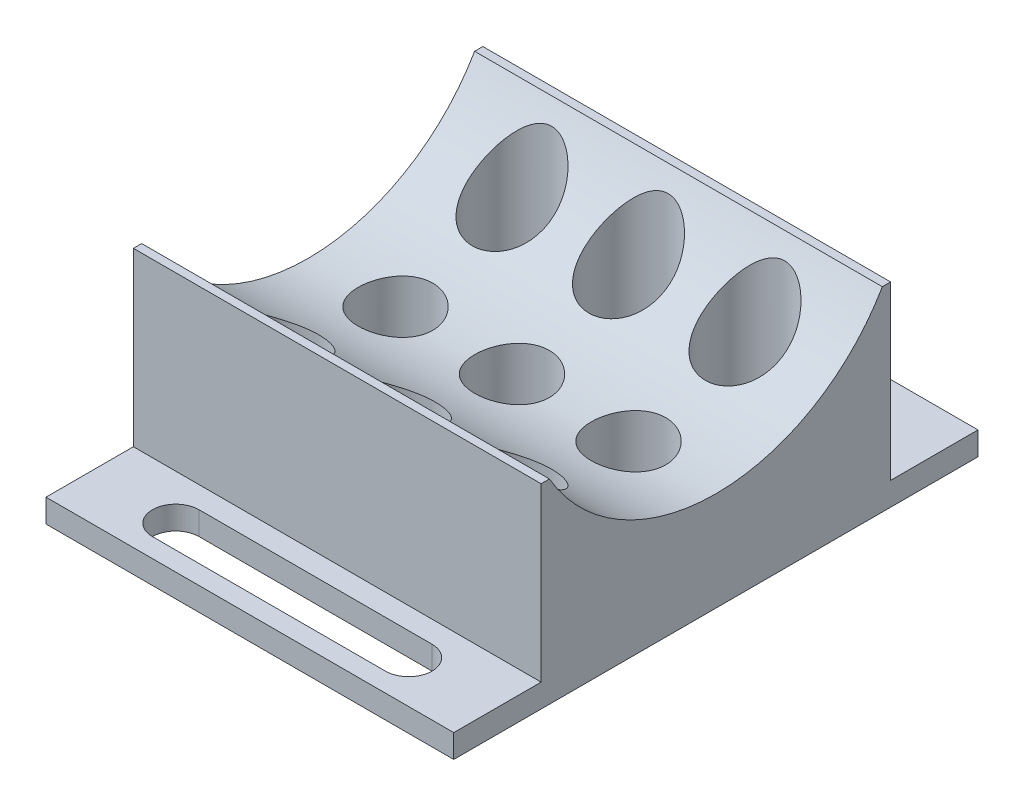
SolidWorks part; units mm, degrees
ref_plane "Front Plane" through (0, 0, 0) normal (0, 0, 1) x (1, 0, 0)
ref_plane "Top Plane" through (0, 0, 0) normal (0, 1, 0) x (1, 0, 0)
ref_plane "Right Plane" through (0, 0, 0) normal (1, 0, 0) x (0, 0, -1)
sketch "Sketch8" plane through (0, 0, 0) normal (0, 1, 0) x (1, 0, 0)
  line L1 (-17.5, -15) -> (17.5, -15)
  line L2 (-17.5, -15) -> (-17.5, 15)
  line L3 (-17.5, 15) -> (17.5, 15)
  line L4 (17.5, -15) -> (17.5, 15)
  line L5 (-17.5, -15) -> (17.5, 15) construction
  line L6 (-17.5, 15) -> (17.5, -15) construction
  point P0 (0, 0)
extrude "Boss-Extrude7" add sketch "Sketch8" along normal blind 80
sketch "Sketch10" plane through (0, 0, 0) normal (1, 0, 0) x (0, 0, -1)
  line L0 (0, 0) -> (0, 40) construction
  circle A0 centre (0, 40) radius 16.5
extrude "Cut-Extrude3" cut sketch "Sketch10" against normal through all and the other way through all
sketch "Sketch11" plane through (0, 0, 0) normal (1, 0, 0) x (0, 0, -1)
  line L1 (19.1682, 48.25) -> (-19.1682, 48.25)
  line L2 (19.1682, 48.25) -> (19.1682, 31.75)
  line L3 (19.1682, 31.75) -> (-19.1682, 31.75)
  line L4 (-19.1682, 48.25) -> (-19.1682, 31.75)
  line L5 (19.1682, 48.25) -> (-19.1682, 31.75) construction
  line L6 (19.1682, 31.75) -> (-19.1682, 48.25) construction
  point P0 (0, 40)
extrude "Cut-Extrude4" cut sketch "Sketch11" against normal through all both and the other way through all
sketch "Sketch12" plane through (0, 0, 0) normal (1, 0, 0) x (0, 0, -1)
  line L1 (17.3515, 0) -> (-16.4734, 0)
  line L2 (17.3515, 0) -> (17.3515, 15)
  line L3 (17.3515, 15) -> (-16.4734, 15)
  line L4 (-16.4734, 0) -> (-16.4734, 15)
extrude "Cut-Extrude5" cut sketch "Sketch12" against normal through all both and the other way through all
sketch "Sketch13" plane through (0, 0, 0) normal (1, 0, 0) x (0, 0, -1)
  line L1 (-29.3401, 40.0643) -> (16.2017, 40.0643)
  line L2 (-29.3401, 40.0643) -> (-29.3401, 81.5521)
  line L3 (-29.3401, 81.5521) -> (16.2017, 81.5521)
  line L4 (16.2017, 40.0643) -> (16.2017, 81.5521)
extrude "Cut-Extrude6" cut sketch "Sketch13" against normal through all both and the other way through all
ref_plane "Plane3" through (0, 15, 0) normal (0, -1, 0) x (-1, 0, 0)
sketch "Sketch15" plane through (0, 15, 0) normal (0, -1, 0) x (-1, 0, 0)
  line L1 (17.5, -15) -> (-17.5, -15)
  line L2 (17.5, -15) -> (17.5, -22.5)
  line L3 (17.5, -22.5) -> (-17.5, -22.5)
  line L4 (-17.5, -15) -> (-17.5, -22.5)
  line L5 (17.5, 15) -> (-17.5, 15)
  line L6 (17.5, 15) -> (17.5, 22.5)
  line L7 (17.5, 22.5) -> (-17.5, 22.5)
  line L8 (-17.5, 15) -> (-17.5, 22.5)
extrude "Boss-Extrude9" add sketch "Sketch15" against normal blind 2
sketch "Sketch16" plane through (0, 15, 0) normal (0, -1, 0) x (-1, 0, 0)
  line L0 (17.5, -22.5) -> (-17.5, -15.227) construction
  line L1 (-17.5, 22.5) -> (-17.5, -22.5) construction
  line L2 (-17.5, -22.5) -> (17.5, -15.227) construction
  line L3 (17.5, 22.5) -> (17.5, -22.5) construction
  line L4 (10, -18.8635) -> (-10, -18.8635) construction
  line L5 (10, -20.8635) -> (-10, -20.8635)
  line L6 (10, -16.8635) -> (-10, -16.8635)
  line L7 (17.5, 22.5) -> (-17.5, 15.1069) construction
  line L8 (-17.5, 22.5) -> (17.5, 15.1069) construction
  line L9 (10, 18.8035) -> (-10, 18.8035) construction
  line L10 (10, 16.8035) -> (-10, 16.8035)
  line L11 (10, 20.8035) -> (-10, 20.8035)
  arc A0 (10, -20.8635) -> (10, -16.8635) centre (10, -18.8635) ccw
  arc A1 (-10, -16.8635) -> (-10, -20.8635) centre (-10, -18.8635) ccw
  arc A2 (10, 16.8035) -> (10, 20.8035) centre (10, 18.8035) ccw
  arc A3 (-10, 20.8035) -> (-10, 16.8035) centre (-10, 18.8035) ccw
  point P12 (0, -18.8635)
  point P25 (0, 18.8035)
extrude "Cut-Extrude7" cut sketch "Sketch16" against normal blind 2
ref_plane "Plane5" through (0, 23.5, 0) normal (0, 1, 0) x (1, 0, 0)
sketch "Sketch18" plane through (0, 23.5, 0) normal (0, 1, 0) x (1, 0, 0)
  circle A0 centre (0, 0) radius 3.2
  circle A1 centre (10, 0) radius 3.2
  circle A2 centre (-10, 0) radius 3.2
  dimension "D1" = 2
  dimension "D2" = 2
extrude "Cut-Extrude10" cut sketch "Sketch18" against normal blind 6.4 and the other way through all
sketch "Sketch19" plane through (0, 23.5, 0) normal (0, 1, 0) x (1, 0, 0)
  line L0 (-10, 0) -> (-10, -10) construction
  circle A0 centre (-10, -10) radius 3.4
  circle A1 centre (0, -10) radius 3.4
  circle A2 centre (10, -10) radius 3.4
  circle A3 centre (-10, 10) radius 3.4
  circle A4 centre (0, 10) radius 3.4
  circle A5 centre (10, 10) radius 3.4
  dimension "D1" = 3
  dimension "D2" = 2
ref_plane "Plane6" through (-10, 0, 0) normal (-1, 0, 0) x (0, 0, 1)
sketch "Sketch20" plane through (-10, 0, 0) normal (-1, 0, 0) x (0, 0, 1)
  line L0 (10, 23.5) -> (6.6, 23.5) construction
  line L1 (0, 23.5) -> (10, 23.5) construction
  line L2 (6.6, 23.5) -> (6.6, 27.5032) construction
extrude "Cut-Extrude11" cut sketch "Sketch19" along normal up to next and the other way blind 4.9
